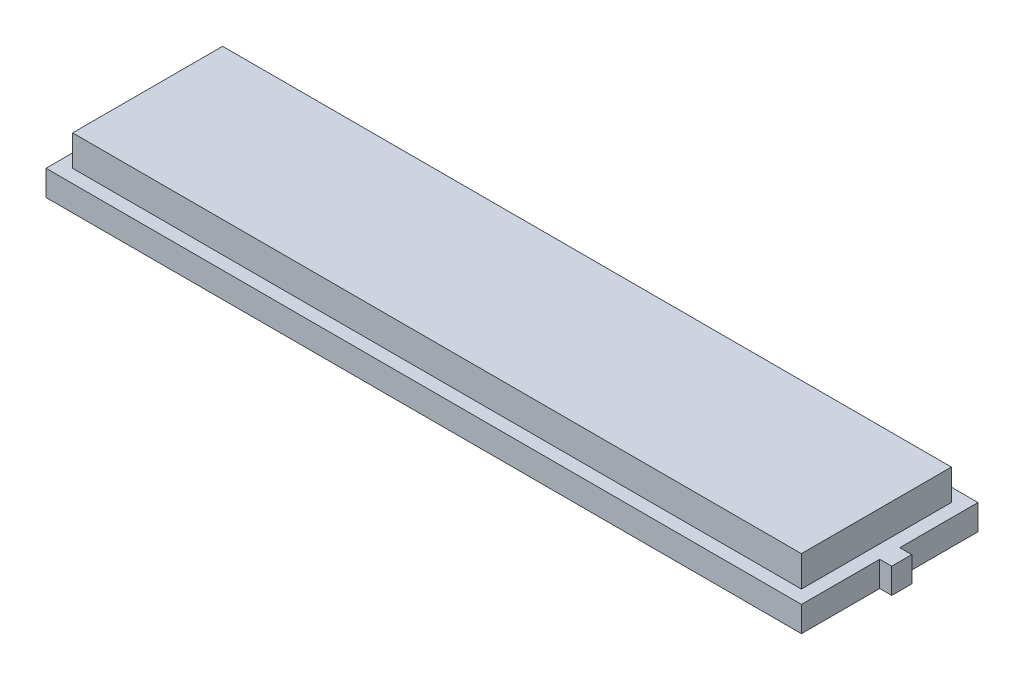
SolidWorks part; units mm, degrees
ref_plane "Front" through (0, 0, 0) normal (0, 0, 1) x (1, 0, 0)
ref_plane "Top" through (0, 0, 0) normal (0, 1, 0) x (1, 0, 0)
ref_plane "Right" through (0, 0, 0) normal (1, 0, 0) x (0, 0, -1)
sketch "Sketch1" plane through (0, 0, 0) normal (0, 1, 0) x (1, 0, 0)
  line L0 (28.31, 6.615) -> (28.31, 0.75)
  line L1 (-28.31, 6.615) -> (28.31, 6.615)
  line L2 (-28.31, 6.615) -> (-28.31, -6.615)
  line L3 (-28.31, -6.615) -> (28.31, -6.615)
  line L4 (28.31, 6.615) -> (28.31, -6.615) construction
  line L5 (28.31, 0.75) -> (29.21, 0.75)
  line L6 (29.21, 0.75) -> (29.21, -0.75)
  line L7 (29.21, -0.75) -> (28.31, -0.75)
  line L8 (28.31, -0.75) -> (28.31, -6.615)
extrude "Boss-Extrude1" add sketch "Sketch1" along normal blind 1.9
sketch "Sketch2" plane through (0, 1.9, 0) normal (0, 1, 0) x (1, 0, 0)
  line L1 (-27.31, 5.62) -> (27.31, 5.62)
  line L2 (-27.31, 5.62) -> (-27.31, -5.62)
  line L3 (-27.31, -5.62) -> (27.31, -5.62)
  line L4 (27.31, 5.62) -> (27.31, -5.62)
extrude "Boss-Extrude2" add sketch "Sketch2" along normal blind 2.3
sketch "Sketch3" plane through (0, 0, 0) normal (0, 1, 0) x (1, 0, 0)
  line L0 (-34.5, -9) -> (-34.5, -16) construction
  line L1 (-34.5, -9) -> (34.5, -9)
  line L2 (-34.5, -9) -> (-34.5, 67.5) construction
  line L3 (-34.5, 67.5) -> (34.5, 67.5) construction
  line L4 (34.5, -9) -> (34.5, 67.5) construction
  line L5 (-34.5, -16) -> (34.5, -16) construction
  line L6 (34.5, -16) -> (34.5, -9) construction
  line L7 (34.5, -9) -> (34.5, 36)
  line L8 (34.5, 36) -> (32, 36) construction
  line L9 (32, 36) -> (32, 46.75) construction
  line L10 (32, 46.75) -> (30, 46.75) construction
  line L11 (30, 46.75) -> (30, 67.5) construction
  line L12 (30, 67.5) -> (-31.3, 67.5)
  line L13 (-31.3, 67.5) -> (-31.3, 40.5) construction
  line L14 (-31.3, 40.5) -> (-34.5, 40.5) construction
  line L15 (-34.5, 40.5) -> (-34.5, -9)
  line L16 (30, 67.5) -> (30, 47.75)
  line L17 (31, 46.75) -> (32, 46.75)
  line L18 (32, 46.75) -> (32, 37)
  line L19 (32.94, 36) -> (34.5, 36)
  line L20 (-31.3, 67.5) -> (-31.3, 41.5)
  line L21 (-32.2185, 40.5) -> (-34.5, 40.5)
  arc A0 (30, 47.75) -> (31, 46.75) centre (31, 47.75) ccw
  arc A1 (32, 37) -> (32.94, 36) centre (33.0019, 37) ccw
  arc A2 (-31.3, 41.5) -> (-32.2185, 40.5) centre (-32.3036, 41.5) cw
